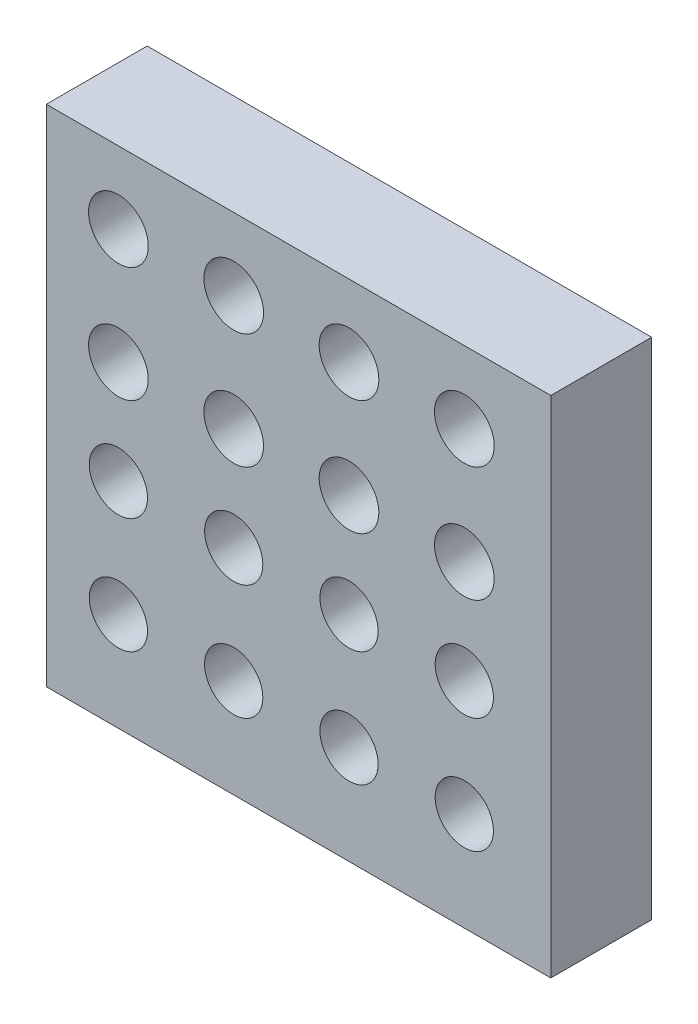
SolidWorks part; units mm, degrees
ref_plane "Front Plane" through (0, 0, 0) normal (0, 0, 1) x (1, 0, 0)
ref_plane "Top Plane" through (0, 0, 0) normal (0, 1, 0) x (1, 0, 0)
ref_plane "Right Plane" through (0, 0, 0) normal (1, 0, 0) x (0, 0, -1)
sketch "Sketch1" plane through (0, 0, 0) normal (0, 0, 1) x (1, 0, 0)
  line L1 (0, 0) -> (35, 0)
  line L2 (0, 0) -> (0, -35)
  line L3 (0, -35) -> (35, -35)
  line L4 (35, 0) -> (35, -35)
  dimension "D1" = 35
  dimension "D2" = 35
extrude "Boss-Extrude1" add sketch "Sketch1" along normal blind 7
sketch "Sketch2" plane through (0, 0, 7) normal (0, 0, 1) x (1, 0, 0)
  line L0 (0, 0) -> (0, -35) construction
  line L1 (35, 0) -> (0, 0) construction
  circle A0 centre (5, -5) radius 2.07
  circle A1 centre (13, -5) radius 2.07
  circle A2 centre (21, -5) radius 2.07
  circle A3 centre (29, -5) radius 2.07
  circle A5 centre (5, -13) radius 2.07
  circle A6 centre (13, -13) radius 2.07
  circle A7 centre (21, -13) radius 2.07
  circle A8 centre (29, -13) radius 2.07
  circle A9 centre (5, -20.1498) radius 2.02
  circle A10 centre (13, -20.1498) radius 2.02
  circle A11 centre (21, -20.1498) radius 2.02
  circle A12 centre (29, -20.1498) radius 2.02
  circle A13 centre (13, -28.1498) radius 2.02
  circle A14 centre (21, -28.1498) radius 2.02
  circle A15 centre (29, -28.1498) radius 2.02
  circle A16 centre (5, -28.1498) radius 2.02
  dimension "D1" = 4.14
  dimension "D2" = 5
  dimension "D5" = 2
  dimension "D6" = 4.04
  dimension "D3" = 5
  dimension "D4" = 4
  dimension "D7" = 4
  dimension "D8" = 2
extrude "Cut-Extrude1" cut sketch "Sketch2" against normal blind 5
